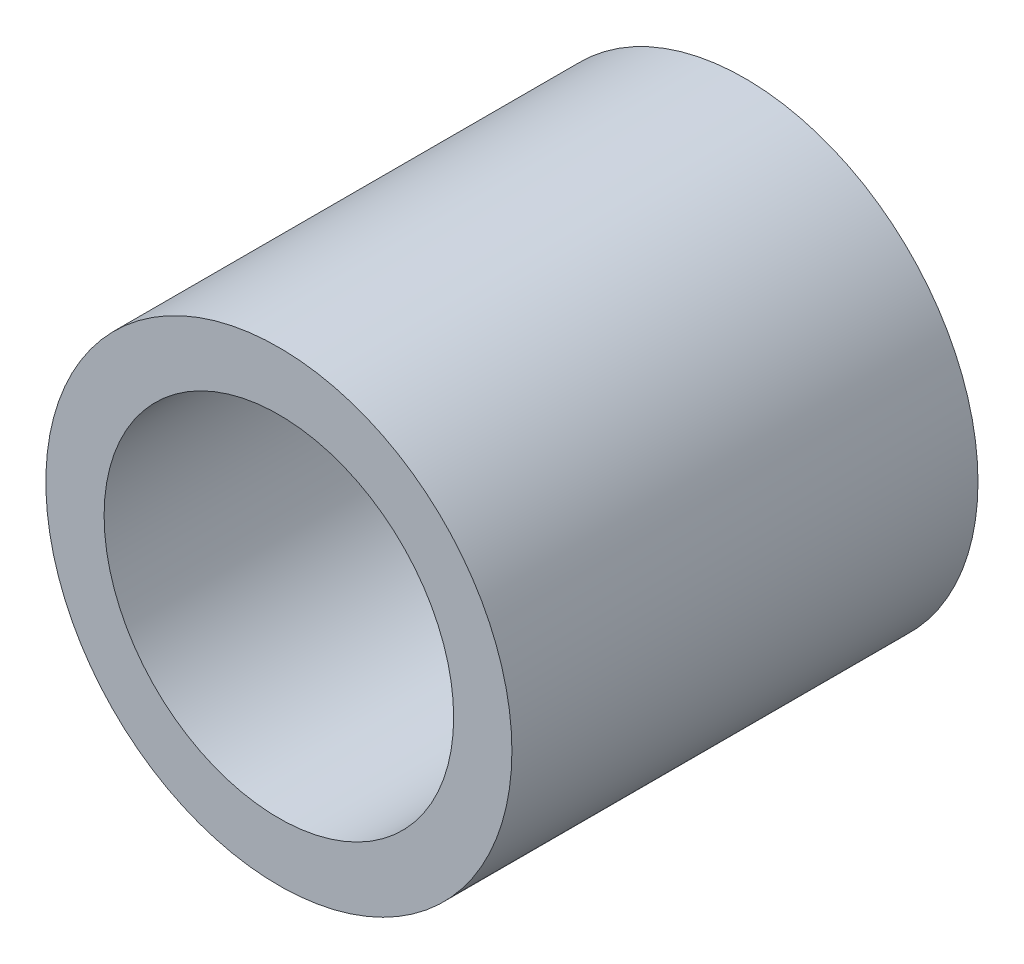
SolidWorks part; units mm, degrees
ref_plane "Front Plane" through (0, 0, 0) normal (0, 0, 1) x (1, 0, 0)
ref_plane "Top Plane" through (0, 0, 0) normal (0, 1, 0) x (1, 0, 0)
ref_plane "Right Plane" through (0, 0, 0) normal (1, 0, 0) x (0, 0, -1)
sketch "Sketch1" plane through (0, 0, 0) normal (0, 0, 1) x (1, 0, 0)
  circle A0 centre (0, 0) radius 2
  circle A1 centre (0, 0) radius 1.5
  dimension "D1" = 4
  dimension "D2" = 3
extrude "Boss-Extrude1" add sketch "Sketch1" along normal blind 4
